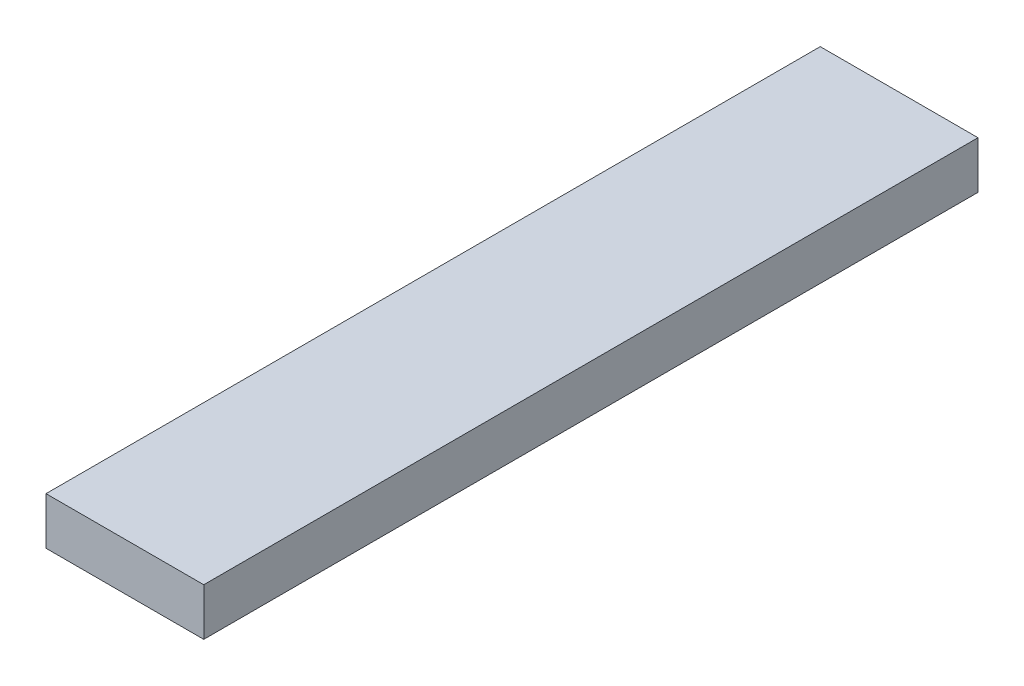
SolidWorks part; units mm, degrees
ref_plane "Front Plane" through (0, 0, 0) normal (0, 0, 1) x (1, 0, 0)
ref_plane "Top Plane" through (0, 0, 0) normal (0, 1, 0) x (1, 0, 0)
ref_plane "Right Plane" through (0, 0, 0) normal (1, 0, 0) x (0, 0, -1)
sketch "Sketch1" plane through (0, 0, 0) normal (0, 1, 0) x (1, 0, 0)
  line L1 (0, 0) -> (10, 0)
  line L2 (0, 0) -> (0, 49.08)
  line L3 (0, 49.08) -> (10, 49.08)
  line L4 (10, 0) -> (10, 49.08)
  dimension "D1" = 49.08
  dimension "D2" = 10
extrude "Boss-Extrude1" add sketch "Sketch1" along normal blind 3
